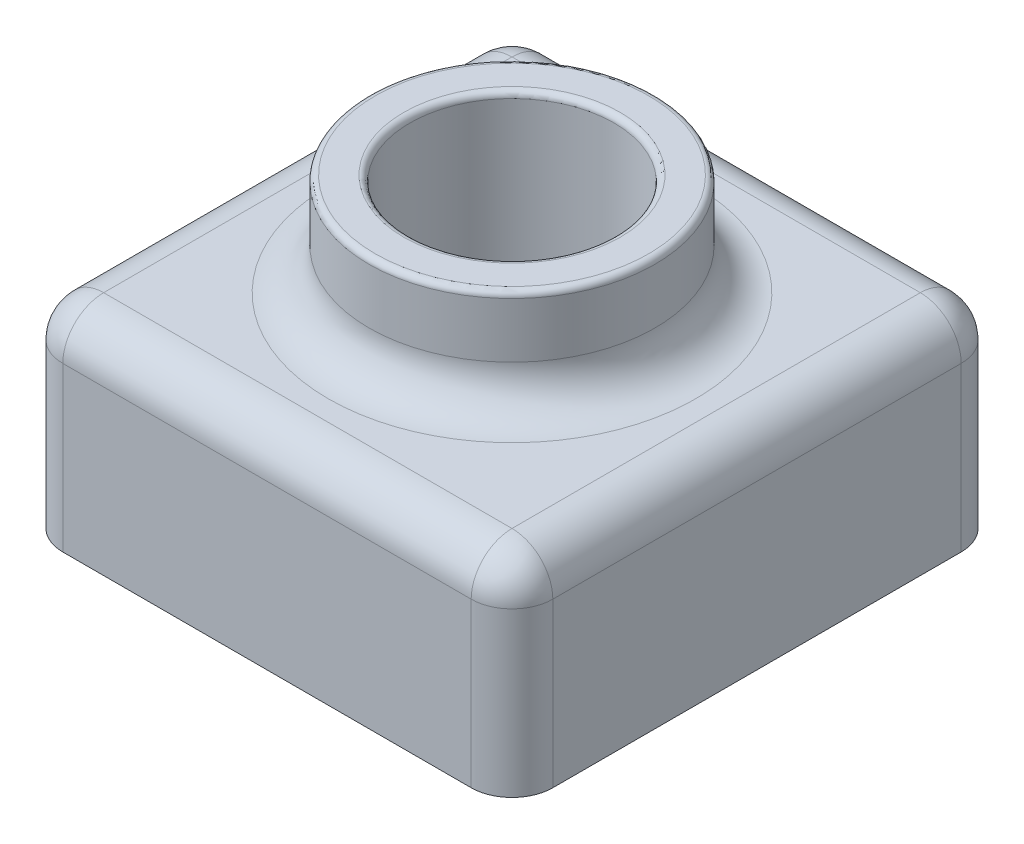
SolidWorks part; units mm, degrees
ref_plane "Front Plane" through (0, 0, 0) normal (0, 0, 1) x (1, 0, 0)
ref_plane "Top Plane" through (0, 0, 0) normal (0, 1, 0) x (1, 0, 0)
ref_plane "Right Plane" through (0, 0, 0) normal (1, 0, 0) x (0, 0, -1)
sketch "Sketch3" plane through (0, 0, 0) normal (0, 1, 0) x (1, 0, 0)
  line L1 (0, 0) -> (120, 0)
  line L2 (0, 0) -> (0, 120)
  line L3 (0, 120) -> (120, 120)
  line L4 (120, 0) -> (120, 120)
  dimension "D1" = 120
  dimension "D2" = 120
extrude "Boss-Extrude2" add sketch "Sketch3" along normal blind 50 contours L2 L1 L4 L3
sketch "Sketch4" plane through (0, 50, 0) normal (0, 1, 0) x (1, 0, 0)
  line L0 (0, 120) -> (120, 120) construction
  line L1 (120, 0) -> (120, 120) construction
  circle A0 centre (60, 60) radius 35
  dimension "D1" = 70
  dimension "D2" = 60
  dimension "D3" = 60
extrude "Boss-Extrude3" add sketch "Sketch4" along normal blind 25 contours A0
sketch "Sketch9" plane through (0, 75, 0) normal (0, 1, 0) x (1, 0, 0)
  circle A0 centre (60, 60) radius 25
  dimension "D1" = 50
extrude "Cut-Extrude3" cut sketch "Sketch9" against normal through all contours A0
fillet "Fillet4" radius 10 9 edges at (120, 50, -60) (60, 50, 0) (0, 50, -60) (60, 50, -120) (60, 50, -25) (120, 25, -120) (0, 25, -120) (0, 25, 0) (120, 25, 0)
fillet "Fillet5" radius 1.5 2 edges at (60, 75, -25) (60, 75, -35)
shell "Shell2" thickness 2
